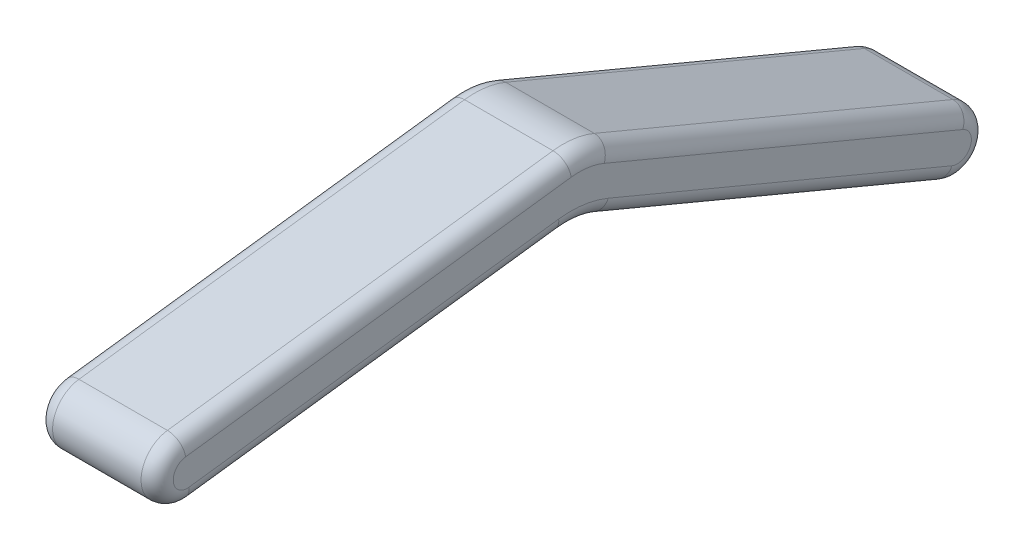
SolidWorks part; units mm, degrees
ref_plane "Front Plane" through (0, 0, 0) normal (0, 0, 1) x (1, 0, 0)
ref_plane "Top Plane" through (0, 0, 0) normal (0, 1, 0) x (1, 0, 0)
ref_plane "Right Plane" through (0, 0, 0) normal (1, 0, 0) x (0, 0, -1)
sketch "Sketch1" plane through (0, 0, 0) normal (1, 0, 0) x (0, 0, -1)
  line L2 (1.4471, 3.4595) -> (-43.1352, 22.1078)
  line L3 (-48.2649, 22.8012) -> (-96.1984, 16.6599)
  line L4 (-1.4471, -3.4595) -> (-44.1754, 14.4132)
  line L5 (-49.3051, 15.1067) -> (-95.2453, 9.2208)
  arc A0 (-1.4471, -3.4595) -> (1.4471, 3.4595) centre (0, 0) ccw
  arc A1 (-96.1984, 16.6599) -> (-95.2453, 9.2208) centre (-95.7219, 12.9404) ccw
  arc A2 (-44.1754, 14.4132) -> (-49.3051, 15.1067) centre (-48.0343, 5.1877) ccw
  arc A3 (-43.1352, 22.1078) -> (-48.2649, 22.8012) centre (-46.9941, 12.8823) ccw
  dimension "D1" = 7.5
  dimension "D2" = 10
extrude "Boss-Extrude1" add sketch "Sketch1" along normal mid plane 15
fillet "Fillet1" radius 2 16 edges at (-7.5, 5.4768, 22.8112) (-7.5, -1.4471, -3.4595) (-7.5, 12.7837, 20.8441) (-7.5, 22.7922, 45.6544) (-7.5, 19.7306, 72.2317) (-7.5, 12.4638, 99.4415) (-7.5, 12.1637, 72.2752) (-7.5, 15.0976, 46.6946) (7.5, 12.1637, 72.2752) (7.5, 12.4638, 99.4415) (7.5, 19.7306, 72.2317) (7.5, 22.7922, 45.6544) (7.5, 12.7837, 20.8441) (7.5, -1.4471, -3.4595) (7.5, 5.4768, 22.8112) (7.5, 15.0976, 46.6946)
